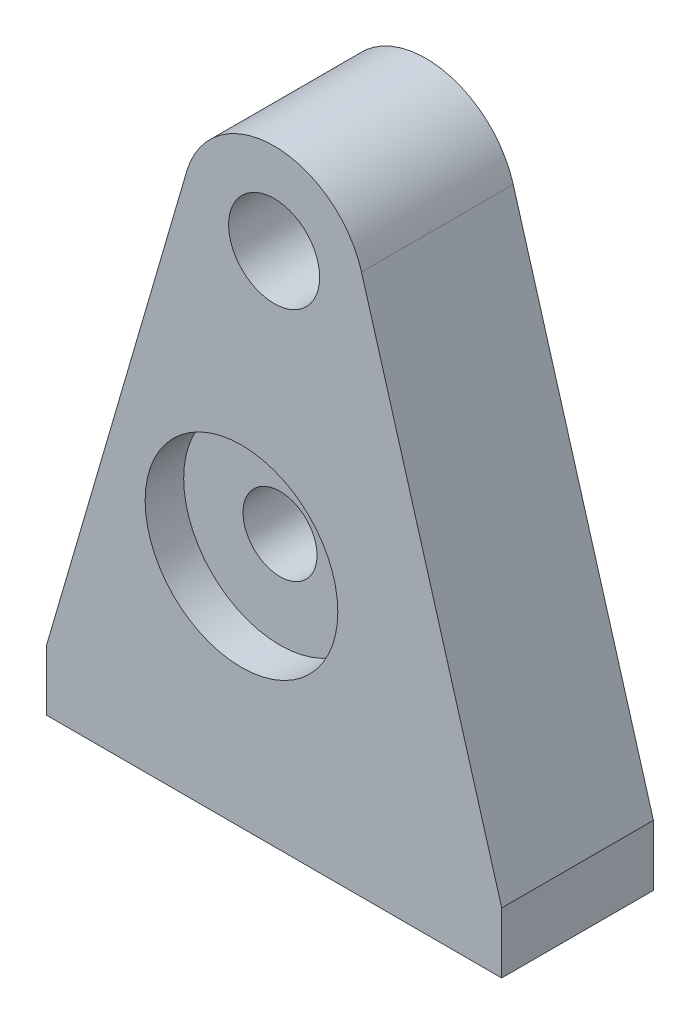
SolidWorks part; units mm, degrees
ref_plane "Front Plane" through (0, 0, 0) normal (0, 0, 1) x (1, 0, 0)
ref_plane "Top Plane" through (0, 0, 0) normal (0, 1, 0) x (1, 0, 0)
ref_plane "Right Plane" through (0, 0, 0) normal (1, 0, 0) x (0, 0, -1)
sketch "Sketch1" plane through (0, 0, 0) normal (0, 0, 1) x (1, 0, 0)
  line L0 (0, 0) -> (15, 0) construction
  line L1 (15, 0) -> (10.38, 15.84)
  line L2 (0, 0) -> (4.62, 15.84)
  line L4 (0, 0) -> (15, 0) construction
  line L5 (0, 0) -> (0, -2)
  line L6 (0, -2) -> (15, -2)
  line L7 (15, 0) -> (15, -2)
  arc A0 (10.38, 15.84) -> (4.62, 15.84) centre (7.5, 15) ccw
  circle A1 centre (7.5, 15) radius 1.5
  dimension "D4" = 3
  dimension "D5" = 3
  dimension "D1" = 15
  dimension "D2" = 15
  dimension "D3" = 2
extrude "Boss-Extrude1" add sketch "Sketch1" along normal blind 5
hole_wizard "CBORE for #2 Hex Machine Screw1" positions "Sketch2" profile "Sketch3" counterbore size "#2" standard "ANSI Inch" end condition through all
sketch "Sketch2" plane through (0, 0, 5) normal (0, 0, 1) x (1, 0, 0)
  point P0 (6.4234, 5.7502)
sketch "Sketch3" plane through (6.4234, 5.7502, 5) normal (1, 0, 0) x (0, -1, 0)
  line L0 (0, 0) -> (0, 5)
  line L1 (0, 5) -> (1.2192, 5)
  line L3 (1.2192, 5) -> (1.2192, 1.27)
  line L4 (1.2192, 1.27) -> (3.175, 1.27)
  line L5 (3.175, 1.27) -> (3.175, 0)
  line L7 (3.175, 0) -> (0, 0)
  line L11 (0, -6.35) -> (0, 107.95) construction
  dimension "Thru Hole Dia." = 2.4384
  dimension "Thru Hole Depth" = 5
  dimension "C'Bore Dia." = 6.35
  dimension "C'Bore Depth" = 1.27
